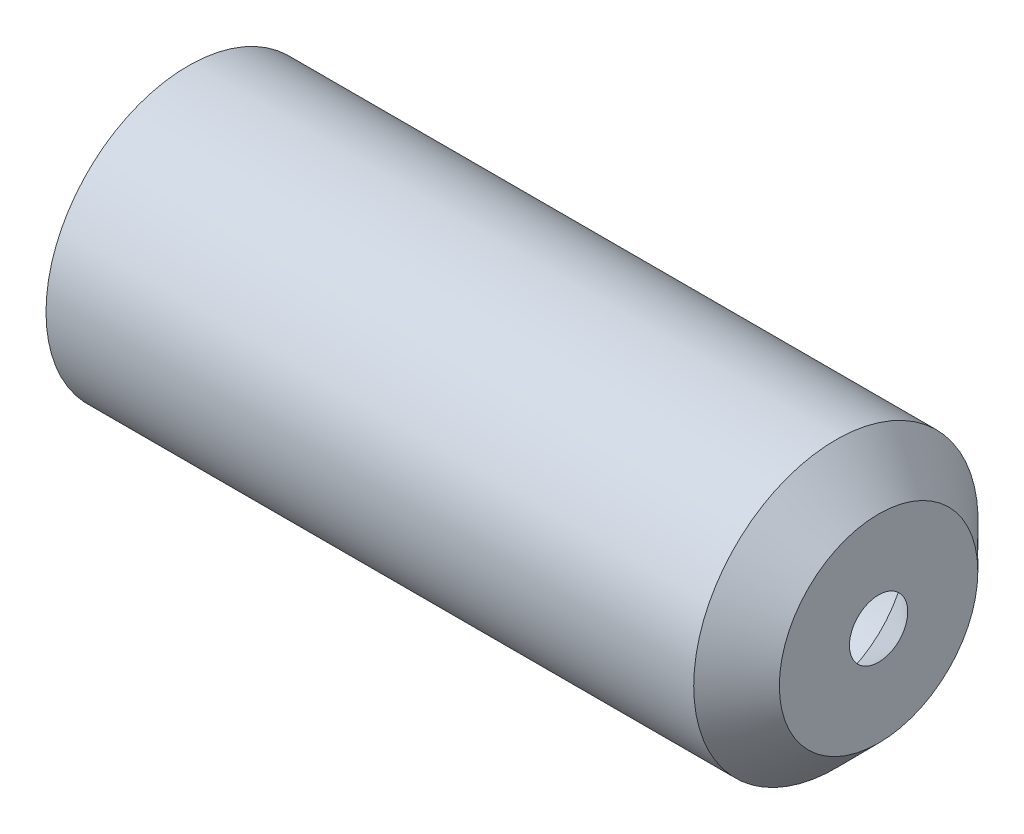
SolidWorks part; units mm, degrees
material "Nichel"
ref_plane "Piano frontale" through (0, 0, 0) normal (0, 0, 1) x (1, 0, 0)
ref_plane "Piano superiore" through (0, 0, 0) normal (0, 1, 0) x (1, 0, 0)
ref_plane "Piano destro" through (0, 0, 0) normal (1, 0, 0) x (0, 0, -1)
sketch "Schizzo1" plane through (0, 0, 0) normal (0, 0, 1) x (1, 0, 0)
  line L0 (-139.6602, 18.8) -> (-12.6602, 18.8)
  line L1 (-12.6602, 18.8) -> (0.1398, 5.9)
  line L3 (0.1398, 20.0975) -> (-8.4953, 28.8)
  line L4 (-8.4953, 28.8) -> (-139.6602, 28.8)
  line L5 (-139.6602, 28.8) -> (-139.6602, 18.8)
  line L6 (-0.2521, 0) -> (0.1825, 0) construction
  line L7 (0.1398, 5.9) -> (0.1398, 20.0975)
  dimension "D1" = 5.9
  dimension "D2" = 18.8
  dimension "D3" = 10
  dimension "D4" = 10
  dimension "D5" = 12.8
  dimension "D6" = 127
revolve "Rivoluzione1" add sketch "Schizzo1" angle 360 about L6
